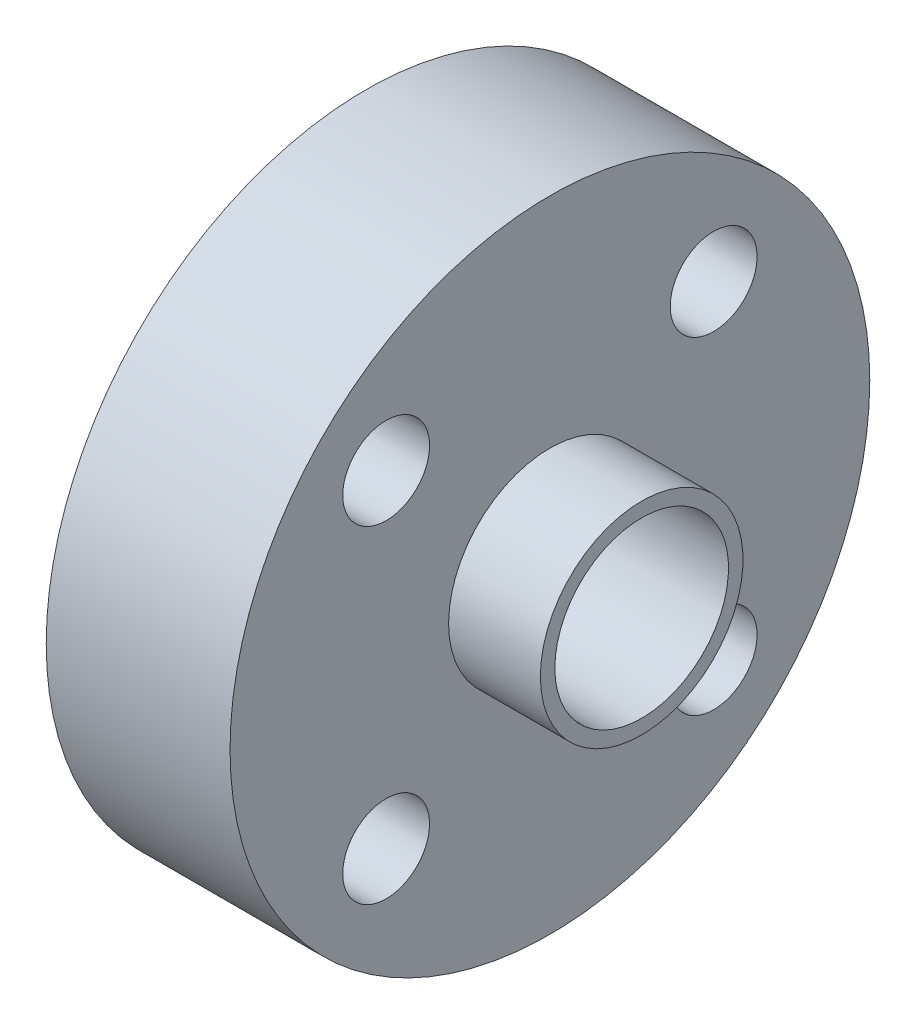
SolidWorks part; units mm, degrees
ref_plane "Plan de face" through (0, 0, 0) normal (0, 0, 1) x (1, 0, 0)
ref_plane "Plan de dessus" through (0, 0, 0) normal (0, 1, 0) x (1, 0, 0)
ref_plane "Plan de droite" through (0, 0, 0) normal (1, 0, 0) x (0, 0, -1)
sketch "Esquisse1" plane through (0, 0, 0) normal (0, 1, 0) x (1, 0, 0)
  line L0 (-53.297, 0) -> (66.3939, 0) construction
  line L1 (-40.2001, 0) -> (-40.2001, 4.7)
  line L2 (-40.2001, 4.7) -> (-37.0201, 4.7)
  line L3 (-37.0201, 4.7) -> (-37.0201, 11.05)
  line L4 (-37.0201, 11.05) -> (-30.6701, 11.05)
  line L5 (-30.6701, 11.05) -> (-30.6701, 3.5)
  line L6 (-30.6701, 3.5) -> (-27.5001, 3.5)
  line L7 (-27.5001, 3.5) -> (-27.5001, 0)
  line L8 (-27.5001, 0) -> (-40.2001, 0)
  dimension "D1" = 3.18
  dimension "D2" = 9.53
  dimension "D3" = 12.7
  dimension "D4" = 4.7
  dimension "D5" = 3.5
  dimension "D6" = 11.05
revolve "Révolution1" add sketch "Esquisse1" angle 360 about L0
sketch "Esquisse2" plane through (-40.2001, 0, 0) normal (-1, 0, 0) x (0, 0, 1)
  circle A0 centre (0, 0) radius 3
  dimension "D1" = 6
extrude "Enlèv. mat.-Extru.1" cut sketch "Esquisse2" against normal through all
sketch "Esquisse3" plane through (-37.0201, 0, 0) normal (-1, 0, 0) x (0, 0, 1)
  line L0 (0, 0) -> (-5.6569, 5.6569) construction
  line L1 (0, -55) -> (0, 55) construction
  circle A0 centre (-5.6569, 5.6569) radius 1.5
  dimension "D1" = 3
  dimension "D2" = 45
  dimension "D3" = 8
extrude "Enlèv. mat.-Extru.2" cut sketch "Esquisse3" against normal blind 10
pattern_circular "Répétition circulaire1" count 4 every 90 about axis through (0, 0, 0) along (1, 0, 0) of "Enlèv. mat.-Extru.2"
sketch "Esquisse5" plane through (0, 0, 0) normal (0, 0, 1) x (1, 0, 0)
  line L2 (-43.9255, 0) -> (-22.3265, 0) construction
  line L4 (-30.6701, -11.05) -> (-30.6701, 11.05) construction
  circle A0 centre (-33.8451, 0) radius 2.5
  dimension "D1" = 5
  dimension "D2" = 0
  dimension "D3" = 3.175
extrude "Enlèv. mat.-Extru.3" cut sketch "Esquisse5" against normal through all contours A0
